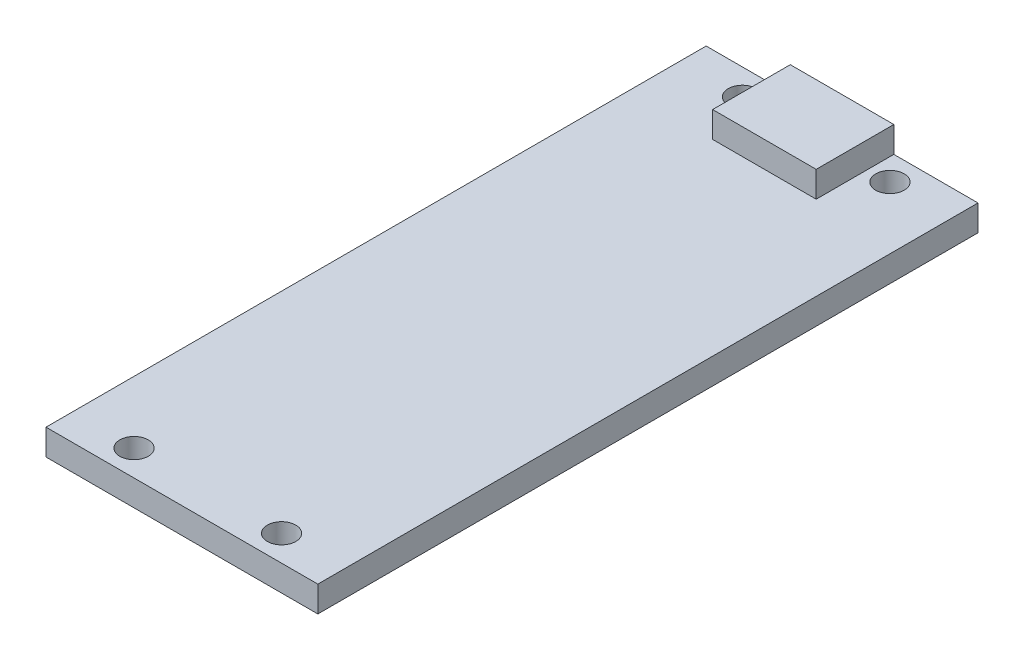
SolidWorks part; units mm, degrees
ref_plane "Front Plane" through (0, 0, 0) normal (0, 0, 1) x (1, 0, 0)
ref_plane "Top Plane" through (0, 0, 0) normal (0, 1, 0) x (1, 0, 0)
ref_plane "Right Plane" through (0, 0, 0) normal (1, 0, 0) x (0, 0, -1)
sketch "Sketch1" plane through (0, 0, 0) normal (0, 1, 0) x (1, 0, 0)
  line L1 (-10.5, 25.5) -> (10.5, 25.5)
  line L2 (-10.5, 25.5) -> (-10.5, -25.5)
  line L3 (-10.5, -25.5) -> (10.5, -25.5)
  line L4 (10.5, 25.5) -> (10.5, -25.5)
  dimension "D1" = 21
  dimension "D2" = 51
  dimension "D3" = 10.5
  dimension "D4" = 25.5
extrude "Boss-Extrude1" add sketch "Sketch1" along normal blind 2
sketch "Sketch2" plane through (0, 2, 0) normal (0, 1, 0) x (1, 0, 0)
  line L0 (10.5, 25.5) -> (-10.5, 25.5) construction
  line L1 (-4, 25.5) -> (4, 25.5)
  line L2 (-4, 25.5) -> (-4, 19.5)
  line L3 (-4, 19.5) -> (4, 19.5)
  line L4 (4, 25.5) -> (4, 19.5)
  dimension "D1" = 8
  dimension "D2" = 4
  dimension "D3" = 6
extrude "Boss-Extrude2" add sketch "Sketch2" along normal blind 2
sketch "Sketch3" plane through (0, 2, 0) normal (0, 1, 0) x (1, 0, 0)
  line L0 (-10.5, -25.5) -> (10.5, -25.5) construction
  line L1 (-4, 25.5) -> (-10.5, 25.5) construction
  circle A0 centre (-5.7, 23.5) radius 1.1
  circle A1 centre (5.7, 23.5) radius 1.1
  circle A2 centre (-5.7, -23.5) radius 1.1
  circle A3 centre (5.7, -23.5) radius 1.1
  point P8 (0, 0)
  point P11 (-3.9594, -15.7694)
  dimension "D1" = 2.2
  dimension "D2" = 2.2
  dimension "D3" = 2.2
  dimension "D4" = 2.2
  dimension "D5" = 11.4
  dimension "D6" = 5.7
  dimension "D7" = 11.4
  dimension "D8" = 5.7
  dimension "D9" = 2
  dimension "D10" = 2
  dimension "D11" = 2
  dimension "D12" = 47
extrude "Cut-Extrude1" cut sketch "Sketch3" against normal blind 2
